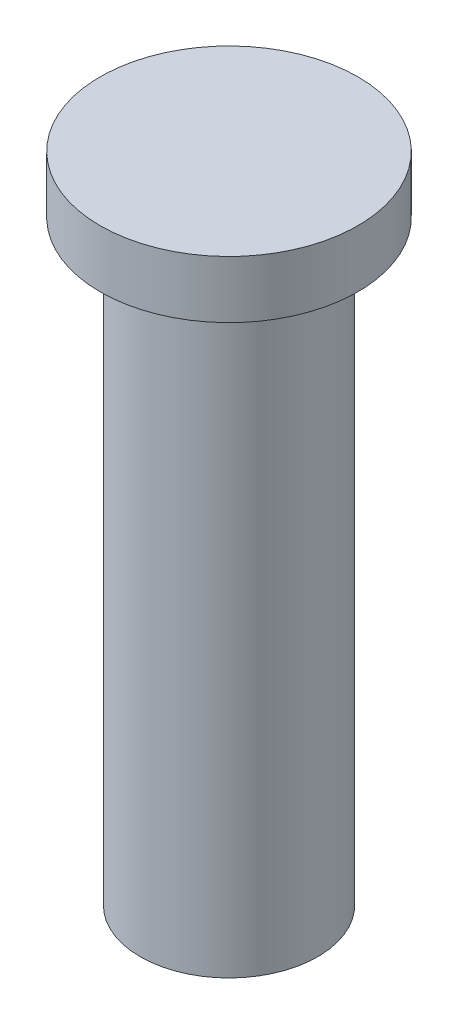
SolidWorks part; units mm, degrees
ref_plane "Front Plane" through (0, 0, 0) normal (0, 0, 1) x (1, 0, 0)
ref_plane "Top Plane" through (0, 0, 0) normal (0, 1, 0) x (1, 0, 0)
ref_plane "Right Plane" through (0, 0, 0) normal (1, 0, 0) x (0, 0, -1)
sketch "Sketch1" plane through (0, 0, 0) normal (0, 1, 0) x (1, 0, 0)
  circle A0 centre (0, 0) radius 3.937
  dimension "D1" = 7.874
extrude "Boss-Extrude1" add sketch "Sketch1" along normal blind 26.416
sketch "Sketch2" plane through (0, 26.416, 0) normal (0, 1, 0) x (1, 0, 0)
  circle A0 centre (0, 0) radius 5.715
  dimension "D1" = 11.43
extrude "Boss-Extrude2" add sketch "Sketch2" along normal blind 2.54
